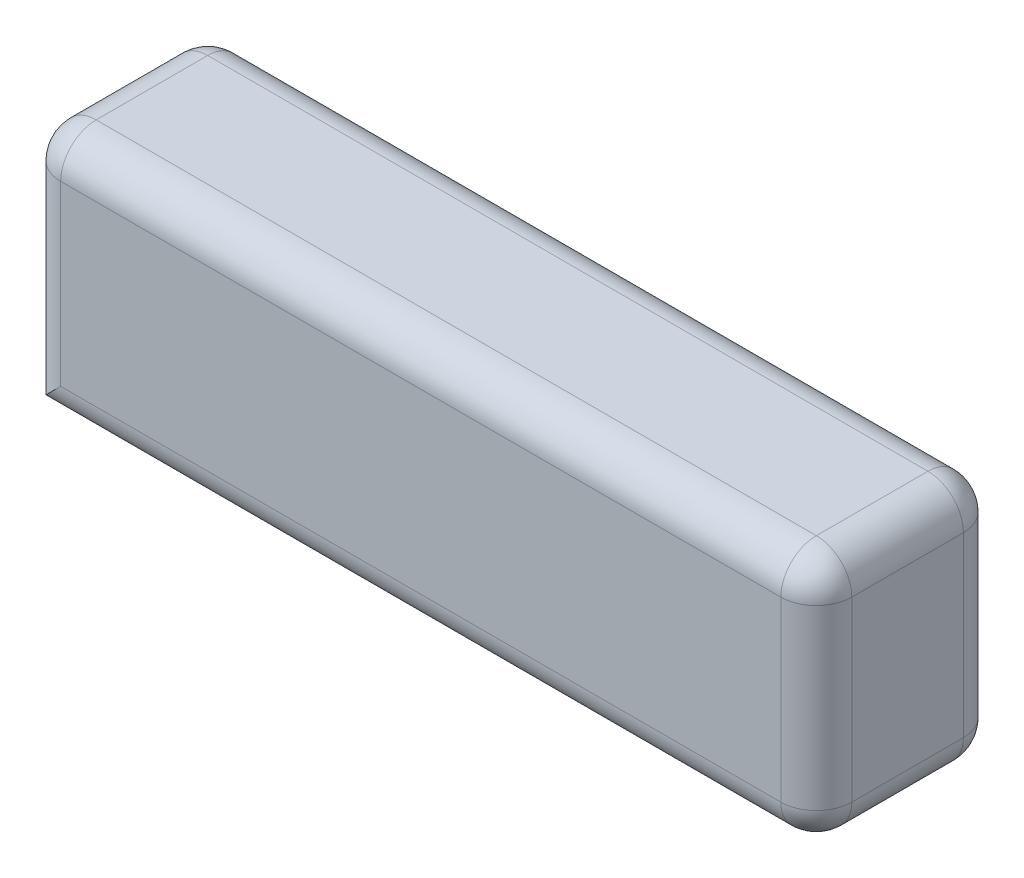
SolidWorks part; units mm, degrees
ref_plane "Front Plane" through (0, 0, 0) normal (0, 0, 1) x (1, 0, 0)
ref_plane "Top Plane" through (0, 0, 0) normal (0, 1, 0) x (1, 0, 0)
ref_plane "Right Plane" through (0, 0, 0) normal (1, 0, 0) x (0, 0, -1)
sketch "Sketch1" plane through (0, 0, 0) normal (0, 0, 1) x (1, 0, 0)
  line L1 (0, 0) -> (156, 0)
  line L2 (0, 0) -> (0, 49)
  line L3 (0, 49) -> (156, 49)
  line L4 (156, 0) -> (156, 49)
  dimension "D1" = 49
  dimension "D2" = 156
extrude "Boss-Extrude1" add sketch "Sketch1" along normal blind 36
fillet "Fillet1" radius 7 11 edges at (0, 24.5, 0) (78, 0, 0) (0, 49, 18) (0, 24.5, 36) (78, 0, 36) (156, 0, 18) (156, 24.5, 36) (156, 24.5, 0) (78, 49, 0) (78, 49, 36) (156, 49, 18)
